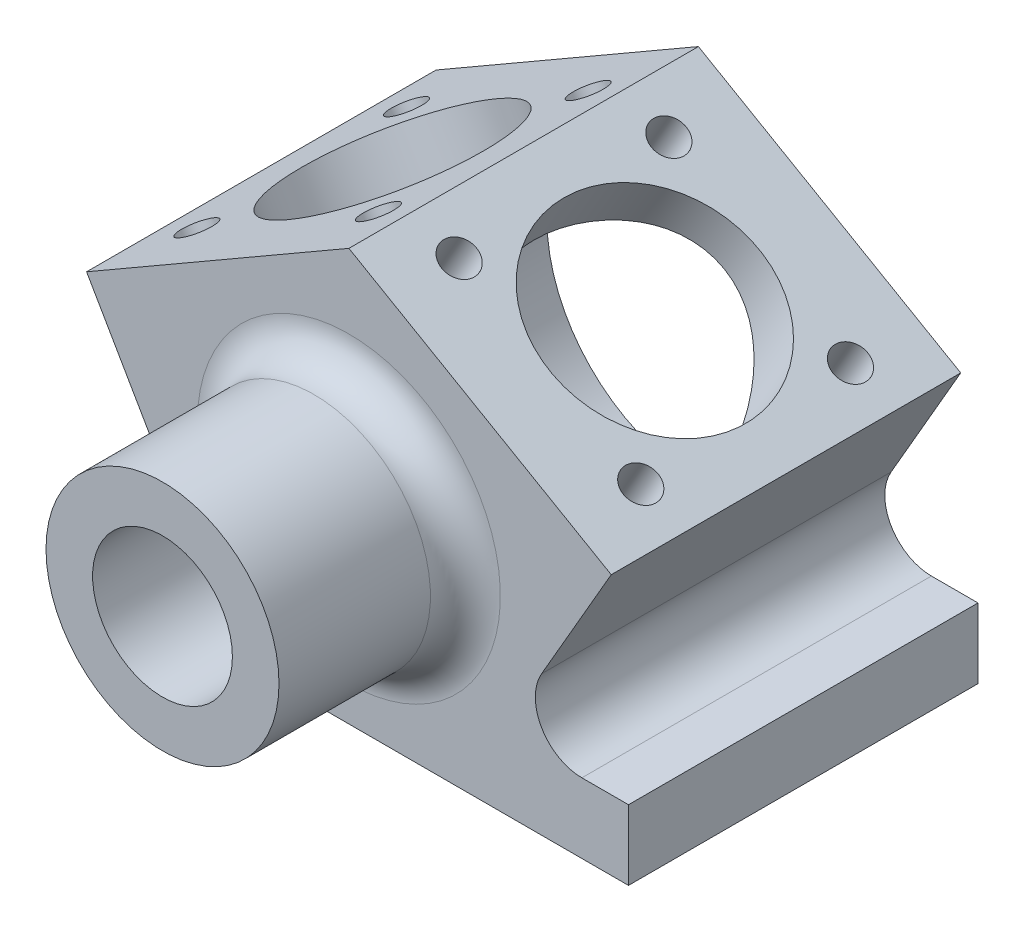
SolidWorks part; units mm, degrees
material "AISI 304"
ref_plane "Front Plane" through (0, 0, 0) normal (0, 0, 1) x (1, 0, 0)
ref_plane "Top Plane" through (0, 0, 0) normal (0, 1, 0) x (1, 0, 0)
ref_plane "Right Plane" through (0, 0, 0) normal (1, 0, 0) x (0, 0, -1)
sketch "Sketch1" plane through (0, 0, 0) normal (0, 0, 1) x (1, 0, 0)
  line L0 (-12, 0) -> (12, 0)
  line L1 (12, 0) -> (12, 3)
  line L2 (12, 3) -> (10, 3)
  line L3 (8.2679, 6) -> (11.2583, 11.1795)
  line L4 (0, 0) -> (0, 20.9331) construction
  line L5 (11.2583, 11.1795) -> (0, 17.6795)
  line L6 (-11.2583, 11.1795) -> (0, 17.6795)
  line L7 (-8.2679, 6) -> (-11.2583, 11.1795)
  line L8 (-12, 3) -> (-10, 3)
  line L9 (-12, 0) -> (-12, 3)
  arc A0 (10, 3) -> (8.2679, 6) centre (10, 5) cw
  arc A1 (-10, 3) -> (-8.2679, 6) centre (-10, 5) ccw
  point P4 (0, 0)
  dimension "D3" = 2
  dimension "D1" = 24
  dimension "D2" = 3
  dimension "D4" = 2
  dimension "D5" = 60
  dimension "D6" = 90
  dimension "D7" = 13
extrude "Boss-Extrude1" add sketch "Sketch1" along normal mid plane 15
sketch "Sketch2" plane through (0, 0, 7.5) normal (0, 0, 1) x (1, 0, 0)
  line L0 (-12, 0) -> (12, 0) construction
  line L1 (0, 0) -> (0, 16.0881) construction
  circle A0 centre (0, 8) radius 5
  dimension "D1" = 10
  dimension "D2" = 8
extrude "Boss-Extrude2" add sketch "Sketch2" along normal blind 8
sketch "Sketch3" plane through (0, 0, -7.5) normal (0, 0, -1) x (-1, 0, 0)
  circle A0 centre (0, 8) radius 6.5
  dimension "D1" = 13
extrude "Cut-Extrude1" cut sketch "Sketch3" against normal blind 13
sketch "Sketch4" plane through (0, 0, 15.5) normal (0, 0, 1) x (1, 0, 0)
  circle A0 centre (0, 8) radius 3
  dimension "D1" = 6
extrude "Cut-Extrude2" cut sketch "Sketch4" against normal up to next
sketch "Sketch5" plane through (7.6554, 13.2596, 0) normal (0.5, 0.866, 0) x (0.866, -0.5, 0)
  line L1 (4.1603, 7.5) -> (-8.8397, 7.5) construction
  line L3 (4.1603, -7.5) -> (4.1603, 7.5) construction
  circle A0 centre (-2.3397, 0) radius 4.5
  dimension "D3" = 9
  dimension "D1" = 7.5
  dimension "D2" = 6.5
extrude "Cut-Extrude3" cut sketch "Sketch5" against normal up to next
mirror "Mirror1" about plane through (0, 0, 0) normal (1, 0, 0) of "Cut-Extrude3"
sketch "Sketch6" plane through (7.6554, 13.2596, 0) normal (0.5, 0.866, 0) x (0.866, -0.5, 0)
  line L0 (-2.3397, 0) -> (-18.7987, 0) construction
  line L1 (-2.3397, 0) -> (-2.3397, 9.5337) construction
  circle A0 centre (-6.8397, 4.5) radius 0.75
  circle A1 centre (2.1603, 4.5) radius 0.75
  circle A2 centre (2.1603, -4.5) radius 0.75
  circle A3 centre (-6.8397, -4.5) radius 0.75
  dimension "D3" = 1.5
  dimension "D1" = 9
  dimension "D2" = 9
extrude "Cut-Extrude4" cut sketch "Sketch6" against normal blind 2
mirror "Mirror2" about plane through (0, 0, 0) normal (1, 0, 0) of "Cut-Extrude4"
fillet "Fillet1" radius 1.5 1 edges at (-5, 8, 7.5)
